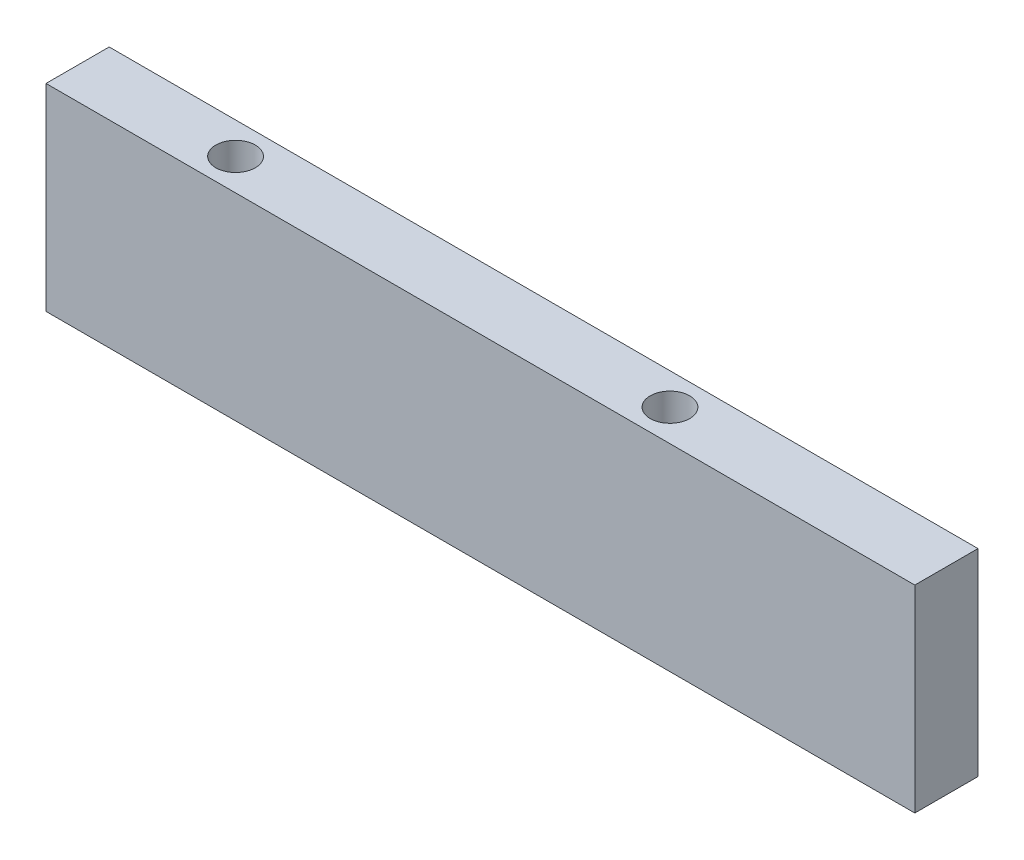
SolidWorks part; units mm, degrees
ref_plane "Front Plane" through (0, 0, 0) normal (0, 0, 1) x (1, 0, 0)
ref_plane "Top Plane" through (0, 0, 0) normal (0, 1, 0) x (1, 0, 0)
ref_plane "Right Plane" through (0, 0, 0) normal (1, 0, 0) x (0, 0, -1)
sketch "Sketch1" plane through (0, 0, 0) normal (0, 1, 0) x (1, 0, 0)
  line L1 (0, 0) -> (110, 0)
  line L2 (0, 0) -> (0, 8)
  line L3 (0, 8) -> (110, 8)
  line L4 (110, 0) -> (110, 8)
  dimension "D1" = 8
  dimension "D2" = 110
extrude "Boss-Extrude1" add sketch "Sketch1" along normal blind 25
sketch "Sketch2" plane through (0, 25, 0) normal (0, 1, 0) x (1, 0, 0)
  line L0 (0, 8) -> (0, 0) construction
  line L1 (110, 0) -> (110, 8) construction
  line L2 (110, 8) -> (0, 8) construction
  circle A0 centre (20, 4) radius 2.5
  circle A1 centre (75, 4) radius 2.5
  dimension "D3" = 5
  dimension "D4" = 5
  dimension "D1" = 20
  dimension "D2" = 35
  dimension "D5" = 4
extrude "Cut-Extrude1" cut sketch "Sketch2" against normal through all
